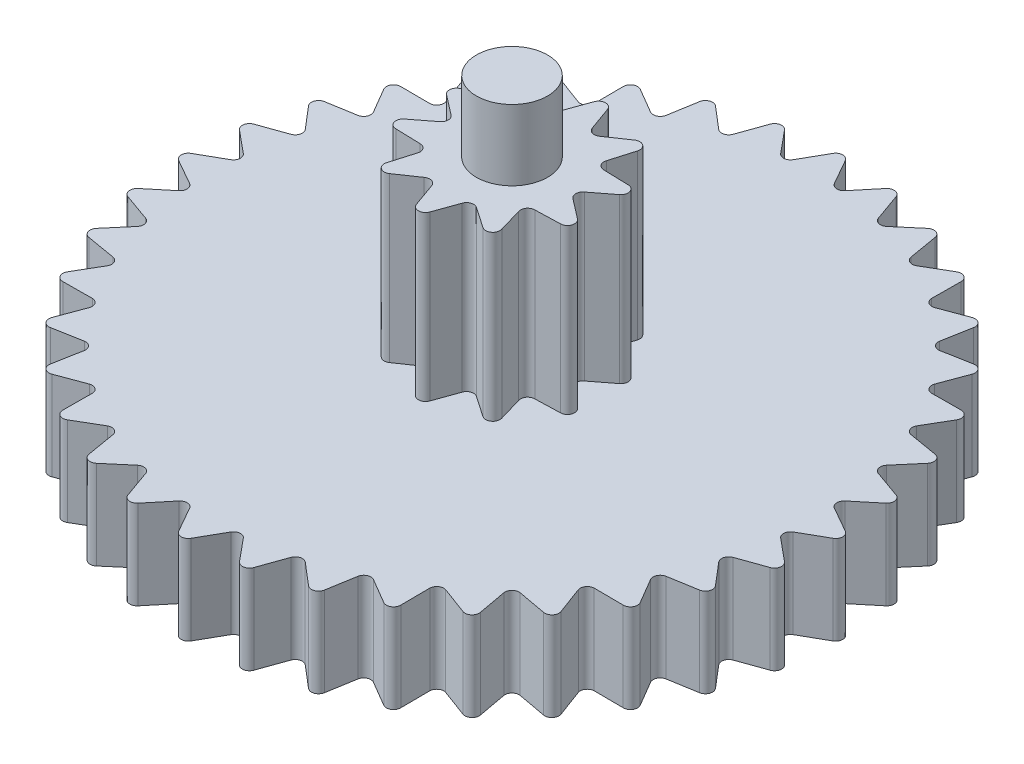
SolidWorks part; units mm, degrees
ref_plane "Front Plane" through (0, 0, 0) normal (0, 0, 1) x (1, 0, 0)
ref_plane "Top Plane" through (0, 0, 0) normal (0, 1, 0) x (1, 0, 0)
ref_plane "Right Plane" through (0, 0, 0) normal (1, 0, 0) x (0, 0, -1)
sketch "Sketch1" plane through (0, 0, 0) normal (0, 1, 0) x (1, 0, 0)
  line L0 (-8.2272, 4.75) -> (-8.9271, 3.2492) construction
  line L1 (0, 9.5) -> (-1.6497, 9.3557) construction
  line L2 (-1.6497, 9.3557) -> (-3.2492, 8.9271) construction
  line L3 (-3.2492, 8.9271) -> (-4.75, 8.2272) construction
  line L4 (-4.75, 8.2272) -> (-6.1065, 7.2774) construction
  line L5 (-6.1065, 7.2774) -> (-7.2774, 6.1065) construction
  line L6 (-7.2774, 6.1065) -> (-8.2272, 4.75) construction
  line L7 (-8.9271, 3.2492) -> (-9.3557, 1.6497) construction
  line L8 (-9.3557, 1.6497) -> (-9.5, 0) construction
  line L9 (-9.5, 0) -> (-9.3557, -1.6497) construction
  line L10 (-9.3557, -1.6497) -> (-8.9271, -3.2492) construction
  line L11 (-8.9271, -3.2492) -> (-8.2272, -4.75) construction
  line L12 (-8.2272, -4.75) -> (-7.2774, -6.1065) construction
  line L13 (-7.2774, -6.1065) -> (-6.1065, -7.2774) construction
  line L14 (-6.1065, -7.2774) -> (-4.75, -8.2272) construction
  line L15 (-4.75, -8.2272) -> (-3.2492, -8.9271) construction
  line L16 (-3.2492, -8.9271) -> (-1.6497, -9.3557) construction
  line L17 (-1.6497, -9.3557) -> (0, -9.5) construction
  line L18 (0, -9.5) -> (1.6497, -9.3557) construction
  line L19 (1.6497, -9.3557) -> (3.2492, -8.9271) construction
  line L20 (3.2492, -8.9271) -> (4.75, -8.2272) construction
  line L21 (4.75, -8.2272) -> (6.1065, -7.2774) construction
  line L22 (6.1065, -7.2774) -> (7.2774, -6.1065) construction
  line L23 (7.2774, -6.1065) -> (8.2272, -4.75) construction
  line L24 (8.2272, -4.75) -> (8.9271, -3.2492) construction
  line L25 (8.9271, -3.2492) -> (9.3557, -1.6497) construction
  line L26 (9.3557, -1.6497) -> (9.5, 0) construction
  line L27 (9.5, 0) -> (9.3557, 1.6497) construction
  line L28 (9.3557, 1.6497) -> (8.9271, 3.2492) construction
  line L29 (8.9271, 3.2492) -> (8.2272, 4.75) construction
  line L30 (8.2272, 4.75) -> (7.2774, 6.1065) construction
  line L31 (7.2774, 6.1065) -> (6.1065, 7.2774) construction
  line L32 (6.1065, 7.2774) -> (4.75, 8.2272) construction
  line L33 (4.75, 8.2272) -> (3.2492, 8.9271) construction
  line L34 (3.2492, 8.9271) -> (1.6497, 9.3557) construction
  line L35 (1.6497, 9.3557) -> (0, 9.5) construction
  line L36 (0, 9.5) -> (0, -9.5) construction
  line L37 (0, 9.5) -> (-0.7202, 8.2324) construction
  line L38 (-0.8248, 9.4278) -> (-0.7202, 8.2324) construction
  line L39 (0, 9.5) -> (0.7202, 8.2324) construction
  line L40 (0.7202, 8.2324) -> (0.8248, 9.4278) construction
  line L41 (1.4237, 9.0826) -> (0.901, 8.4508)
  line L42 (0.1751, 9.1918) -> (0.5802, 8.4789)
  line L43 (-0.1751, 9.1918) -> (-0.5802, 8.4789)
  line L44 (1.7686, 9.0218) -> (2.0437, 8.2493)
  line L45 (2.9792, 8.6974) -> (2.3547, 8.166)
  line L46 (3.3083, 8.5776) -> (3.4452, 7.7691)
  line L47 (4.4443, 8.0479) -> (3.737, 7.633)
  line L48 (4.7476, 7.8728) -> (4.7419, 7.0528)
  line L49 (5.7743, 7.1539) -> (5.0057, 6.8681)
  line L50 (6.0425, 6.9288) -> (5.8946, 6.1223)
  line L51 (6.9288, 6.0425) -> (6.1223, 5.8946)
  line L52 (7.1539, 5.7743) -> (6.8681, 5.0057)
  line L53 (7.8728, 4.7476) -> (7.0528, 4.7419)
  line L54 (8.0479, 4.4443) -> (7.633, 3.737)
  line L55 (8.5776, 3.3083) -> (7.7691, 3.4452)
  line L56 (8.6974, 2.9792) -> (8.166, 2.3547)
  line L57 (9.0218, 1.7686) -> (8.2493, 2.0437)
  line L58 (9.0826, 1.4237) -> (8.4508, 0.901)
  line L59 (9.1918, 0.1751) -> (8.4789, 0.5802)
  line L60 (9.1918, -0.1751) -> (8.4789, -0.5802)
  line L61 (9.0826, -1.4237) -> (8.4508, -0.901)
  line L62 (9.0218, -1.7686) -> (8.2493, -2.0437)
  line L63 (8.6974, -2.9792) -> (8.166, -2.3547)
  line L64 (8.5776, -3.3083) -> (7.7691, -3.4452)
  line L65 (8.0479, -4.4443) -> (7.633, -3.737)
  line L66 (7.8728, -4.7476) -> (7.0528, -4.7419)
  line L67 (7.1539, -5.7743) -> (6.8681, -5.0057)
  line L68 (6.9288, -6.0425) -> (6.1223, -5.8946)
  line L69 (6.0425, -6.9288) -> (5.8946, -6.1223)
  line L70 (5.7743, -7.1539) -> (5.0057, -6.8681)
  line L71 (4.7476, -7.8728) -> (4.7419, -7.0528)
  line L72 (4.4443, -8.0479) -> (3.737, -7.633)
  line L73 (3.3083, -8.5776) -> (3.4452, -7.7691)
  line L74 (2.9792, -8.6974) -> (2.3547, -8.166)
  line L75 (1.7686, -9.0218) -> (2.0437, -8.2493)
  line L76 (1.4237, -9.0826) -> (0.901, -8.4508)
  line L77 (0.1751, -9.1918) -> (0.5802, -8.4789)
  line L78 (-0.1751, -9.1918) -> (-0.5802, -8.4789)
  line L79 (-1.4237, -9.0826) -> (-0.901, -8.4508)
  line L80 (-1.7686, -9.0218) -> (-2.0437, -8.2493)
  line L81 (-2.9792, -8.6974) -> (-2.3547, -8.166)
  line L82 (-3.3083, -8.5776) -> (-3.4452, -7.7691)
  line L83 (-4.4443, -8.0479) -> (-3.737, -7.633)
  line L84 (-4.7476, -7.8728) -> (-4.7419, -7.0528)
  line L85 (-5.7743, -7.1539) -> (-5.0057, -6.8681)
  line L86 (-6.0425, -6.9288) -> (-5.8946, -6.1223)
  line L87 (-6.9288, -6.0425) -> (-6.1223, -5.8946)
  line L88 (-7.1539, -5.7743) -> (-6.8681, -5.0057)
  line L89 (-7.8728, -4.7476) -> (-7.0528, -4.7419)
  line L90 (-8.0479, -4.4443) -> (-7.633, -3.737)
  line L91 (-8.5776, -3.3083) -> (-7.7691, -3.4452)
  line L92 (-8.6974, -2.9792) -> (-8.166, -2.3547)
  line L93 (-9.0218, -1.7686) -> (-8.2493, -2.0437)
  line L94 (-9.0826, -1.4237) -> (-8.4508, -0.901)
  line L95 (-9.1918, -0.1751) -> (-8.4789, -0.5802)
  line L96 (-9.1918, 0.1751) -> (-8.4789, 0.5802)
  line L97 (-9.0826, 1.4237) -> (-8.4508, 0.901)
  line L98 (-9.0218, 1.7686) -> (-8.2493, 2.0437)
  line L99 (-8.6974, 2.9792) -> (-8.166, 2.3547)
  line L100 (-8.5776, 3.3083) -> (-7.7691, 3.4452)
  line L101 (-8.0479, 4.4443) -> (-7.633, 3.737)
  line L102 (-7.8728, 4.7476) -> (-7.0528, 4.7419)
  line L103 (-7.1539, 5.7743) -> (-6.8681, 5.0057)
  line L104 (-6.9288, 6.0425) -> (-6.1223, 5.8946)
  line L105 (-6.0425, 6.9288) -> (-5.8946, 6.1223)
  line L106 (-5.7743, 7.1539) -> (-5.0057, 6.8681)
  line L107 (-4.7476, 7.8728) -> (-4.7419, 7.0528)
  line L108 (-4.4443, 8.0479) -> (-3.737, 7.633)
  line L109 (-3.3083, 8.5776) -> (-3.4452, 7.7691)
  line L110 (-2.9792, 8.6974) -> (-2.3547, 8.166)
  line L111 (-1.7686, 9.0218) -> (-2.0437, 8.2493)
  line L112 (-1.4237, 9.0826) -> (-0.901, 8.4508)
  line L113 (0.8817, 2.7135) -> (0.5109, 1.5723) construction
  line L114 (0, 3) -> (-1.7634, 2.4271) construction
  line L115 (-1.7634, 2.4271) -> (-2.8532, 0.9271) construction
  line L116 (-2.8532, 0.9271) -> (-2.8532, -0.9271) construction
  line L117 (-2.8532, -0.9271) -> (-1.7634, -2.4271) construction
  line L118 (-1.7634, -2.4271) -> (0, -3) construction
  line L119 (0, -3) -> (1.7634, -2.4271) construction
  line L120 (1.7634, -2.4271) -> (2.8532, -0.9271) construction
  line L121 (2.8532, -0.9271) -> (2.8532, 0.9271) construction
  line L122 (2.8532, 0.9271) -> (1.7634, 2.4271) construction
  line L123 (1.7634, 2.4271) -> (0, 3) construction
  line L124 (-0.8817, 2.7135) -> (-0.5109, 1.5723) construction
  line L125 (0, 3) -> (0, -3) construction
  line L126 (-0.1894, 2.4929) -> (-0.4251, 1.8338)
  line L127 (0.1894, 2.4929) -> (0.4251, 1.8338)
  line L128 (-0.4251, 1.8338) -> (0.4251, 1.8338) construction
  line L129 (-0.1894, 2.4929) -> (0.1894, 2.4929) construction
  line L130 (-0.5795, 1.7836) -> (-0.4251, 1.8338) construction
  line L131 (0.4251, 1.8338) -> (0.5795, 1.7836) construction
  line L132 (1.3121, 2.1281) -> (0.7339, 1.7335)
  line L133 (1.6185, 1.9055) -> (1.4218, 1.2337)
  line L134 (2.3124, 0.9505) -> (1.6127, 0.971)
  line L135 (2.4294, 0.5902) -> (1.8754, 0.1624)
  line L136 (2.4294, -0.5902) -> (1.8754, -0.1624)
  line L137 (2.3124, -0.9505) -> (1.6127, -0.971)
  line L138 (1.6185, -1.9055) -> (1.4218, -1.2337)
  line L139 (1.3121, -2.1281) -> (0.7339, -1.7335)
  line L140 (0.1894, -2.4929) -> (0.4251, -1.8338)
  line L141 (-0.1894, -2.4929) -> (-0.4251, -1.8338)
  line L142 (-1.3121, -2.1281) -> (-0.7339, -1.7335)
  line L143 (-1.6185, -1.9055) -> (-1.4218, -1.2337)
  line L144 (-2.3124, -0.9505) -> (-1.6127, -0.971)
  line L145 (-2.4294, -0.5902) -> (-1.8754, -0.1624)
  line L146 (-2.4294, 0.5902) -> (-1.8754, 0.1624)
  line L147 (-2.3124, 0.9505) -> (-1.6127, 0.971)
  line L148 (-1.6185, 1.9055) -> (-1.4218, 1.2337)
  line L149 (-1.3121, 2.1281) -> (-0.7339, 1.7335)
  circle A0 centre (0, 0) radius 9.5 construction
  arc A1 (-0.1751, 9.1918) -> (0.1751, 9.1918) centre (0, 9.0952) cw
  arc A2 (0.5802, 8.4789) -> (0.7335, 8.3838) centre (0.7509, 8.5831) ccw
  arc A3 (-0.5802, 8.4789) -> (-0.7335, 8.3838) centre (-0.7509, 8.5831) cw
  arc A4 (0.901, 8.4508) -> (0.7335, 8.3838) centre (0.7509, 8.5831) cw
  arc A5 (1.4237, 9.0826) -> (1.7686, 9.0218) centre (1.5794, 8.957) cw
  arc A6 (2.0437, 8.2493) -> (2.1782, 8.1291) centre (2.2299, 8.3223) ccw
  arc A7 (2.3547, 8.166) -> (2.1782, 8.1291) centre (2.2299, 8.3223) cw
  arc A8 (2.9792, 8.6974) -> (3.3083, 8.5776) centre (3.1107, 8.5467) cw
  arc A9 (3.4452, 7.7691) -> (3.5567, 7.6273) centre (3.6412, 7.8086) ccw
  arc A10 (3.737, 7.633) -> (3.5567, 7.6273) centre (3.6412, 7.8086) cw
  arc A11 (4.4443, 8.0479) -> (4.7476, 7.8728) centre (4.5476, 7.8767) cw
  arc A12 (4.7419, 7.0528) -> (4.8271, 6.8939) centre (4.9418, 7.0577) ccw
  arc A13 (5.0057, 6.8681) -> (4.8271, 6.8939) centre (4.9418, 7.0577) cw
  arc A14 (5.7743, 7.1539) -> (6.0425, 6.9288) centre (5.8463, 6.9673) cw
  arc A15 (5.8946, 6.1223) -> (5.9509, 5.9509) centre (6.0923, 6.0923) ccw
  arc A16 (6.1223, 5.8946) -> (5.9509, 5.9509) centre (6.0923, 6.0923) cw
  arc A17 (6.9288, 6.0425) -> (7.1539, 5.7743) centre (6.9673, 5.8463) cw
  arc A18 (6.8681, 5.0057) -> (6.8939, 4.8271) centre (7.0577, 4.9418) ccw
  arc A19 (7.0528, 4.7419) -> (6.8939, 4.8271) centre (7.0577, 4.9418) cw
  arc A20 (7.8728, 4.7476) -> (8.0479, 4.4443) centre (7.8767, 4.5476) cw
  arc A21 (7.633, 3.737) -> (7.6273, 3.5567) centre (7.8086, 3.6412) ccw
  arc A22 (7.7691, 3.4452) -> (7.6273, 3.5567) centre (7.8086, 3.6412) cw
  arc A23 (8.5776, 3.3083) -> (8.6974, 2.9792) centre (8.5467, 3.1107) cw
  arc A24 (8.166, 2.3547) -> (8.1291, 2.1782) centre (8.3223, 2.2299) ccw
  arc A25 (8.2493, 2.0437) -> (8.1291, 2.1782) centre (8.3223, 2.2299) cw
  arc A26 (9.0218, 1.7686) -> (9.0826, 1.4237) centre (8.957, 1.5794) cw
  arc A27 (8.4508, 0.901) -> (8.3838, 0.7335) centre (8.5831, 0.7509) ccw
  arc A28 (8.4789, 0.5802) -> (8.3838, 0.7335) centre (8.5831, 0.7509) cw
  arc A29 (9.1918, 0.1751) -> (9.1918, -0.1751) centre (9.0952, 0) cw
  arc A30 (8.4789, -0.5802) -> (8.3838, -0.7335) centre (8.5831, -0.7509) ccw
  arc A31 (8.4508, -0.901) -> (8.3838, -0.7335) centre (8.5831, -0.7509) cw
  arc A32 (9.0826, -1.4237) -> (9.0218, -1.7686) centre (8.957, -1.5794) cw
  arc A33 (8.2493, -2.0437) -> (8.1291, -2.1782) centre (8.3223, -2.2299) ccw
  arc A34 (8.166, -2.3547) -> (8.1291, -2.1782) centre (8.3223, -2.2299) cw
  arc A35 (8.6974, -2.9792) -> (8.5776, -3.3083) centre (8.5467, -3.1107) cw
  arc A36 (7.7691, -3.4452) -> (7.6273, -3.5567) centre (7.8086, -3.6412) ccw
  arc A37 (7.633, -3.737) -> (7.6273, -3.5567) centre (7.8086, -3.6412) cw
  arc A38 (8.0479, -4.4443) -> (7.8728, -4.7476) centre (7.8767, -4.5476) cw
  arc A39 (7.0528, -4.7419) -> (6.8939, -4.8271) centre (7.0577, -4.9418) ccw
  arc A40 (6.8681, -5.0057) -> (6.8939, -4.8271) centre (7.0577, -4.9418) cw
  arc A41 (7.1539, -5.7743) -> (6.9288, -6.0425) centre (6.9673, -5.8463) cw
  arc A42 (6.1223, -5.8946) -> (5.9509, -5.9509) centre (6.0923, -6.0923) ccw
  arc A43 (5.8946, -6.1223) -> (5.9509, -5.9509) centre (6.0923, -6.0923) cw
  arc A44 (6.0425, -6.9288) -> (5.7743, -7.1539) centre (5.8463, -6.9673) cw
  arc A45 (5.0057, -6.8681) -> (4.8271, -6.8939) centre (4.9418, -7.0577) ccw
  arc A46 (4.7419, -7.0528) -> (4.8271, -6.8939) centre (4.9418, -7.0577) cw
  arc A47 (4.7476, -7.8728) -> (4.4443, -8.0479) centre (4.5476, -7.8767) cw
  arc A48 (3.737, -7.633) -> (3.5567, -7.6273) centre (3.6412, -7.8086) ccw
  arc A49 (3.4452, -7.7691) -> (3.5567, -7.6273) centre (3.6412, -7.8086) cw
  arc A50 (3.3083, -8.5776) -> (2.9792, -8.6974) centre (3.1107, -8.5467) cw
  arc A51 (2.3547, -8.166) -> (2.1782, -8.1291) centre (2.2299, -8.3223) ccw
  arc A52 (2.0437, -8.2493) -> (2.1782, -8.1291) centre (2.2299, -8.3223) cw
  arc A53 (1.7686, -9.0218) -> (1.4237, -9.0826) centre (1.5794, -8.957) cw
  arc A54 (0.901, -8.4508) -> (0.7335, -8.3838) centre (0.7509, -8.5831) ccw
  arc A55 (0.5802, -8.4789) -> (0.7335, -8.3838) centre (0.7509, -8.5831) cw
  arc A56 (0.1751, -9.1918) -> (-0.1751, -9.1918) centre (0, -9.0952) cw
  arc A57 (-0.5802, -8.4789) -> (-0.7335, -8.3838) centre (-0.7509, -8.5831) ccw
  arc A58 (-0.901, -8.4508) -> (-0.7335, -8.3838) centre (-0.7509, -8.5831) cw
  arc A59 (-1.4237, -9.0826) -> (-1.7686, -9.0218) centre (-1.5794, -8.957) cw
  arc A60 (-2.0437, -8.2493) -> (-2.1782, -8.1291) centre (-2.2299, -8.3223) ccw
  arc A61 (-2.3547, -8.166) -> (-2.1782, -8.1291) centre (-2.2299, -8.3223) cw
  arc A62 (-2.9792, -8.6974) -> (-3.3083, -8.5776) centre (-3.1107, -8.5467) cw
  arc A63 (-3.4452, -7.7691) -> (-3.5567, -7.6273) centre (-3.6412, -7.8086) ccw
  arc A64 (-3.737, -7.633) -> (-3.5567, -7.6273) centre (-3.6412, -7.8086) cw
  arc A65 (-4.4443, -8.0479) -> (-4.7476, -7.8728) centre (-4.5476, -7.8767) cw
  arc A66 (-4.7419, -7.0528) -> (-4.8271, -6.8939) centre (-4.9418, -7.0577) ccw
  arc A67 (-5.0057, -6.8681) -> (-4.8271, -6.8939) centre (-4.9418, -7.0577) cw
  arc A68 (-5.7743, -7.1539) -> (-6.0425, -6.9288) centre (-5.8463, -6.9673) cw
  arc A69 (-5.8946, -6.1223) -> (-5.9509, -5.9509) centre (-6.0923, -6.0923) ccw
  arc A70 (-6.1223, -5.8946) -> (-5.9509, -5.9509) centre (-6.0923, -6.0923) cw
  arc A71 (-6.9288, -6.0425) -> (-7.1539, -5.7743) centre (-6.9673, -5.8463) cw
  arc A72 (-6.8681, -5.0057) -> (-6.8939, -4.8271) centre (-7.0577, -4.9418) ccw
  arc A73 (-7.0528, -4.7419) -> (-6.8939, -4.8271) centre (-7.0577, -4.9418) cw
  arc A74 (-7.8728, -4.7476) -> (-8.0479, -4.4443) centre (-7.8767, -4.5476) cw
  arc A75 (-7.633, -3.737) -> (-7.6273, -3.5567) centre (-7.8086, -3.6412) ccw
  arc A76 (-7.7691, -3.4452) -> (-7.6273, -3.5567) centre (-7.8086, -3.6412) cw
  arc A77 (-8.5776, -3.3083) -> (-8.6974, -2.9792) centre (-8.5467, -3.1107) cw
  arc A78 (-8.166, -2.3547) -> (-8.1291, -2.1782) centre (-8.3223, -2.2299) ccw
  arc A79 (-8.2493, -2.0437) -> (-8.1291, -2.1782) centre (-8.3223, -2.2299) cw
  arc A80 (-9.0218, -1.7686) -> (-9.0826, -1.4237) centre (-8.957, -1.5794) cw
  arc A81 (-8.4508, -0.901) -> (-8.3838, -0.7335) centre (-8.5831, -0.7509) ccw
  arc A82 (-8.4789, -0.5802) -> (-8.3838, -0.7335) centre (-8.5831, -0.7509) cw
  arc A83 (-9.1918, -0.1751) -> (-9.1918, 0.1751) centre (-9.0952, 0) cw
  arc A84 (-8.4789, 0.5802) -> (-8.3838, 0.7335) centre (-8.5831, 0.7509) ccw
  arc A85 (-8.4508, 0.901) -> (-8.3838, 0.7335) centre (-8.5831, 0.7509) cw
  arc A86 (-9.0826, 1.4237) -> (-9.0218, 1.7686) centre (-8.957, 1.5794) cw
  arc A87 (-8.2493, 2.0437) -> (-8.1291, 2.1782) centre (-8.3223, 2.2299) ccw
  arc A88 (-8.166, 2.3547) -> (-8.1291, 2.1782) centre (-8.3223, 2.2299) cw
  arc A89 (-8.6974, 2.9792) -> (-8.5776, 3.3083) centre (-8.5467, 3.1107) cw
  arc A90 (-7.7691, 3.4452) -> (-7.6273, 3.5567) centre (-7.8086, 3.6412) ccw
  arc A91 (-7.633, 3.737) -> (-7.6273, 3.5567) centre (-7.8086, 3.6412) cw
  arc A92 (-8.0479, 4.4443) -> (-7.8728, 4.7476) centre (-7.8767, 4.5476) cw
  arc A93 (-7.0528, 4.7419) -> (-6.8939, 4.8271) centre (-7.0577, 4.9418) ccw
  arc A94 (-6.8681, 5.0057) -> (-6.8939, 4.8271) centre (-7.0577, 4.9418) cw
  arc A95 (-7.1539, 5.7743) -> (-6.9288, 6.0425) centre (-6.9673, 5.8463) cw
  arc A96 (-6.1223, 5.8946) -> (-5.9509, 5.9509) centre (-6.0923, 6.0923) ccw
  arc A97 (-5.8946, 6.1223) -> (-5.9509, 5.9509) centre (-6.0923, 6.0923) cw
  arc A98 (-6.0425, 6.9288) -> (-5.7743, 7.1539) centre (-5.8463, 6.9673) cw
  arc A99 (-5.0057, 6.8681) -> (-4.8271, 6.8939) centre (-4.9418, 7.0577) ccw
  arc A100 (-4.7419, 7.0528) -> (-4.8271, 6.8939) centre (-4.9418, 7.0577) cw
  arc A101 (-4.7476, 7.8728) -> (-4.4443, 8.0479) centre (-4.5476, 7.8767) cw
  arc A102 (-3.737, 7.633) -> (-3.5567, 7.6273) centre (-3.6412, 7.8086) ccw
  arc A103 (-3.4452, 7.7691) -> (-3.5567, 7.6273) centre (-3.6412, 7.8086) cw
  arc A104 (-3.3083, 8.5776) -> (-2.9792, 8.6974) centre (-3.1107, 8.5467) cw
  arc A105 (-2.3547, 8.166) -> (-2.1782, 8.1291) centre (-2.2299, 8.3223) ccw
  arc A106 (-2.0437, 8.2493) -> (-2.1782, 8.1291) centre (-2.2299, 8.3223) cw
  arc A107 (-1.7686, 9.0218) -> (-1.4237, 9.0826) centre (-1.5794, 8.957) cw
  arc A108 (-0.901, 8.4508) -> (-0.7335, 8.3838) centre (-0.7509, 8.5831) ccw
  circle A109 centre (0, 0) radius 3 construction
  arc A110 (-0.4251, 1.8338) -> (-0.5538, 1.7045) centre (-0.6156, 1.8947) cw
  arc A111 (-0.1894, 2.4929) -> (0.1894, 2.4929) centre (0, 2.4287) cw
  arc A112 (0.5538, 1.7045) -> (0.4251, 1.8338) centre (0.6156, 1.8947) cw
  arc A113 (0.7339, 1.7335) -> (0.5538, 1.7045) centre (0.6156, 1.8947) cw
  arc A114 (1.3121, 2.1281) -> (1.6185, 1.9055) centre (1.4275, 1.9648) cw
  arc A115 (1.4499, 1.0534) -> (1.4218, 1.2337) centre (1.6118, 1.171) cw
  arc A116 (1.6127, 0.971) -> (1.4499, 1.0534) centre (1.6118, 1.171) cw
  arc A117 (2.3124, 0.9505) -> (2.4294, 0.5902) centre (2.3098, 0.7505) cw
  arc A118 (1.7922, 0) -> (1.8754, 0.1624) centre (1.9922, 0) cw
  arc A119 (1.8754, -0.1624) -> (1.7922, 0) centre (1.9922, 0) cw
  arc A120 (2.4294, -0.5902) -> (2.3124, -0.9505) centre (2.3098, -0.7505) cw
  arc A121 (1.4499, -1.0534) -> (1.6127, -0.971) centre (1.6118, -1.171) cw
  arc A122 (1.4218, -1.2337) -> (1.4499, -1.0534) centre (1.6118, -1.171) cw
  arc A123 (1.6185, -1.9055) -> (1.3121, -2.1281) centre (1.4275, -1.9648) cw
  arc A124 (0.5538, -1.7045) -> (0.7339, -1.7335) centre (0.6156, -1.8947) cw
  arc A125 (0.4251, -1.8338) -> (0.5538, -1.7045) centre (0.6156, -1.8947) cw
  arc A126 (0.1894, -2.4929) -> (-0.1894, -2.4929) centre (0, -2.4287) cw
  arc A127 (-0.5538, -1.7045) -> (-0.4251, -1.8338) centre (-0.6156, -1.8947) cw
  arc A128 (-0.7339, -1.7335) -> (-0.5538, -1.7045) centre (-0.6156, -1.8947) cw
  arc A129 (-1.3121, -2.1281) -> (-1.6185, -1.9055) centre (-1.4275, -1.9648) cw
  arc A130 (-1.4499, -1.0534) -> (-1.4218, -1.2337) centre (-1.6118, -1.171) cw
  arc A131 (-1.6127, -0.971) -> (-1.4499, -1.0534) centre (-1.6118, -1.171) cw
  arc A132 (-2.3124, -0.9505) -> (-2.4294, -0.5902) centre (-2.3098, -0.7505) cw
  arc A133 (-1.7922, 0) -> (-1.8754, -0.1624) centre (-1.9922, 0) cw
  arc A134 (-1.8754, 0.1624) -> (-1.7922, 0) centre (-1.9922, 0) cw
  arc A135 (-2.4294, 0.5902) -> (-2.3124, 0.9505) centre (-2.3098, 0.7505) cw
  arc A136 (-1.4499, 1.0534) -> (-1.6127, 0.971) centre (-1.6118, 1.171) cw
  arc A137 (-1.4218, 1.2337) -> (-1.4499, 1.0534) centre (-1.6118, 1.171) cw
  arc A138 (-1.6185, 1.9055) -> (-1.3121, 2.1281) centre (-1.4275, 1.9648) cw
  arc A139 (-0.5538, 1.7045) -> (-0.7339, 1.7335) centre (-0.6156, 1.8947) cw
  point P441 (0, 0)
  dimension "D4" = 0.2
  dimension "D5" = 0.4048
  dimension "D7" = 0.2
  dimension "D6" = 0.2
  dimension "D12" = 0.2
  dimension "D13" = 0.2
  dimension "D14" = 0.2
  dimension "D1" = 19
  dimension "D2" = 0.82
  dimension "D3" = 1.2
  dimension "D8" = 1.6497
  dimension "D10" = 6
  dimension "D11" = 1.2
  dimension "D15" = 0.7
  dimension "D16" = 0.9777
  dimension "D17" = 0.3788
  dimension "D18" = 0.1624
  dimension "D9" = 36
  dimension "D19" = 10
extrude "Boss-Extrude1" add sketch "Sketch1" along normal blind 2.5
sketch "Sketch2" plane through (0, 0, 0) normal (0, 1, 0) x (1, 0, 0)
  line L0 (-2.4294, 0.5902) -> (-1.8754, 0.1624) construction
  line L1 (-1.6127, 0.971) -> (-2.3124, 0.9505) construction
  line L2 (-1.6185, 1.9055) -> (-1.4218, 1.2337) construction
  line L3 (-0.7339, 1.7335) -> (-1.3121, 2.1281) construction
  line L4 (-0.1894, 2.4929) -> (-0.4251, 1.8338) construction
  line L5 (0.4251, 1.8338) -> (0.1894, 2.4929) construction
  line L6 (1.3121, 2.1281) -> (0.7339, 1.7335) construction
  line L7 (1.4218, 1.2337) -> (1.6185, 1.9055) construction
  line L8 (2.3124, 0.9505) -> (1.6127, 0.971) construction
  line L9 (1.8754, 0.1624) -> (2.4294, 0.5902) construction
  line L10 (2.4294, -0.5902) -> (1.8754, -0.1624) construction
  line L11 (1.6127, -0.971) -> (2.3124, -0.9505) construction
  line L12 (1.6185, -1.9055) -> (1.4218, -1.2337) construction
  line L13 (0.7339, -1.7335) -> (1.3121, -2.1281) construction
  line L14 (0.1894, -2.4929) -> (0.4251, -1.8338) construction
  line L15 (-0.4251, -1.8338) -> (-0.1894, -2.4929) construction
  line L16 (-1.3121, -2.1281) -> (-0.7339, -1.7335) construction
  line L17 (-1.4218, -1.2337) -> (-1.6185, -1.9055) construction
  line L18 (-2.3124, -0.9505) -> (-1.6127, -0.971) construction
  line L19 (-1.8754, -0.1624) -> (-2.4294, -0.5902) construction
  line L20 (-2.4294, 0.5902) -> (-1.8754, 0.1624)
  line L21 (-1.6127, 0.971) -> (-2.3124, 0.9505)
  line L22 (-1.6185, 1.9055) -> (-1.4218, 1.2337)
  line L23 (-0.7339, 1.7335) -> (-1.3121, 2.1281)
  line L24 (-0.1894, 2.4929) -> (-0.4251, 1.8338)
  line L25 (0.4251, 1.8338) -> (0.1894, 2.4929)
  line L26 (1.3121, 2.1281) -> (0.7339, 1.7335)
  line L27 (1.4218, 1.2337) -> (1.6185, 1.9055)
  line L28 (2.3124, 0.9505) -> (1.6127, 0.971)
  line L29 (1.8754, 0.1624) -> (2.4294, 0.5902)
  line L30 (2.4294, -0.5902) -> (1.8754, -0.1624)
  line L31 (1.6127, -0.971) -> (2.3124, -0.9505)
  line L32 (1.6185, -1.9055) -> (1.4218, -1.2337)
  line L33 (0.7339, -1.7335) -> (1.3121, -2.1281)
  line L34 (0.1894, -2.4929) -> (0.4251, -1.8338)
  line L35 (-0.4251, -1.8338) -> (-0.1894, -2.4929)
  line L36 (-1.3121, -2.1281) -> (-0.7339, -1.7335)
  line L37 (-1.4218, -1.2337) -> (-1.6185, -1.9055)
  line L38 (-2.3124, -0.9505) -> (-1.6127, -0.971)
  line L39 (-1.8754, -0.1624) -> (-2.4294, -0.5902)
  arc A0 (-2.3124, 0.9505) -> (-2.4294, 0.5902) centre (-2.3098, 0.7505) ccw construction
  arc A1 (-1.6127, 0.971) -> (-1.4218, 1.2337) centre (-1.6118, 1.171) ccw construction
  arc A2 (-1.3121, 2.1281) -> (-1.6185, 1.9055) centre (-1.4275, 1.9648) ccw construction
  arc A3 (-0.7339, 1.7335) -> (-0.4251, 1.8338) centre (-0.6156, 1.8947) ccw construction
  arc A4 (0.1894, 2.4929) -> (-0.1894, 2.4929) centre (0, 2.4287) ccw construction
  arc A5 (0.4251, 1.8338) -> (0.7339, 1.7335) centre (0.6156, 1.8947) ccw construction
  arc A6 (1.6185, 1.9055) -> (1.3121, 2.1281) centre (1.4275, 1.9648) ccw construction
  arc A7 (1.4218, 1.2337) -> (1.6127, 0.971) centre (1.6118, 1.171) ccw construction
  arc A8 (2.4294, 0.5902) -> (2.3124, 0.9505) centre (2.3098, 0.7505) ccw construction
  arc A9 (1.8754, 0.1624) -> (1.8754, -0.1624) centre (1.9922, 0) ccw construction
  arc A10 (2.3124, -0.9505) -> (2.4294, -0.5902) centre (2.3098, -0.7505) ccw construction
  arc A11 (1.6127, -0.971) -> (1.4218, -1.2337) centre (1.6118, -1.171) ccw construction
  arc A12 (1.3121, -2.1281) -> (1.6185, -1.9055) centre (1.4275, -1.9648) ccw construction
  arc A13 (0.7339, -1.7335) -> (0.4251, -1.8338) centre (0.6156, -1.8947) ccw construction
  arc A14 (-0.1894, -2.4929) -> (0.1894, -2.4929) centre (0, -2.4287) ccw construction
  arc A15 (-1.6185, -1.9055) -> (-1.3121, -2.1281) centre (-1.4275, -1.9648) ccw construction
  arc A16 (-1.4218, -1.2337) -> (-1.6127, -0.971) centre (-1.6118, -1.171) ccw construction
  arc A17 (-2.4294, -0.5902) -> (-2.3124, -0.9505) centre (-2.3098, -0.7505) ccw construction
  arc A18 (-1.8754, -0.1624) -> (-1.8754, 0.1624) centre (-1.9922, 0) ccw construction
  arc A19 (-0.4251, -1.8338) -> (-0.7339, -1.7335) centre (-0.6156, -1.8947) ccw construction
  arc A20 (-2.3124, 0.9505) -> (-2.4294, 0.5902) centre (-2.3098, 0.7505) ccw
  arc A21 (-1.6127, 0.971) -> (-1.4218, 1.2337) centre (-1.6118, 1.171) ccw
  arc A22 (-1.3121, 2.1281) -> (-1.6185, 1.9055) centre (-1.4275, 1.9648) ccw
  arc A23 (-0.7339, 1.7335) -> (-0.4251, 1.8338) centre (-0.6156, 1.8947) ccw
  arc A24 (0.1894, 2.4929) -> (-0.1894, 2.4929) centre (0, 2.4287) ccw
  arc A25 (0.4251, 1.8338) -> (0.7339, 1.7335) centre (0.6156, 1.8947) ccw
  arc A26 (1.6185, 1.9055) -> (1.3121, 2.1281) centre (1.4275, 1.9648) ccw
  arc A27 (1.4218, 1.2337) -> (1.6127, 0.971) centre (1.6118, 1.171) ccw
  arc A28 (2.4294, 0.5902) -> (2.3124, 0.9505) centre (2.3098, 0.7505) ccw
  arc A29 (1.8754, 0.1624) -> (1.8754, -0.1624) centre (1.9922, 0) ccw
  arc A30 (2.3124, -0.9505) -> (2.4294, -0.5902) centre (2.3098, -0.7505) ccw
  arc A31 (1.6127, -0.971) -> (1.4218, -1.2337) centre (1.6118, -1.171) ccw
  arc A32 (1.3121, -2.1281) -> (1.6185, -1.9055) centre (1.4275, -1.9648) ccw
  arc A33 (0.7339, -1.7335) -> (0.4251, -1.8338) centre (0.6156, -1.8947) ccw
  arc A34 (-0.1894, -2.4929) -> (0.1894, -2.4929) centre (0, -2.4287) ccw
  arc A35 (-1.6185, -1.9055) -> (-1.3121, -2.1281) centre (-1.4275, -1.9648) ccw
  arc A36 (-1.4218, -1.2337) -> (-1.6127, -0.971) centre (-1.6118, -1.171) ccw
  arc A37 (-2.4294, -0.5902) -> (-2.3124, -0.9505) centre (-2.3098, -0.7505) ccw
  arc A38 (-1.8754, -0.1624) -> (-1.8754, 0.1624) centre (-1.9922, 0) ccw
  arc A39 (-0.4251, -1.8338) -> (-0.7339, -1.7335) centre (-0.6156, -1.8947) ccw
  circle A40 centre (0, 0) radius 1
  dimension "D1" = 2
extrude "Boss-Extrude2" add sketch "Sketch2" along normal blind 7.1
sketch "Sketch3" plane through (0, 0, 0) normal (0, 1, 0) x (1, 0, 0)
  circle A0 centre (0, 0) radius 1 construction
  circle A1 centre (0, 0) radius 1
extrude "Boss-Extrude3" add sketch "Sketch3" along normal blind 9.08 and the other way blind 2.6
fillet "Fillet1" radius 1 1 edges at (0, -2.6, 1)
sketch "Axis" plane through (0, 0, 0) normal (1, 0, 0) x (0, 0, -1)
  line L0 (0, 0) -> (0, 9.08) construction
  line L1 (1, 9.08) -> (-1, 9.08) construction
